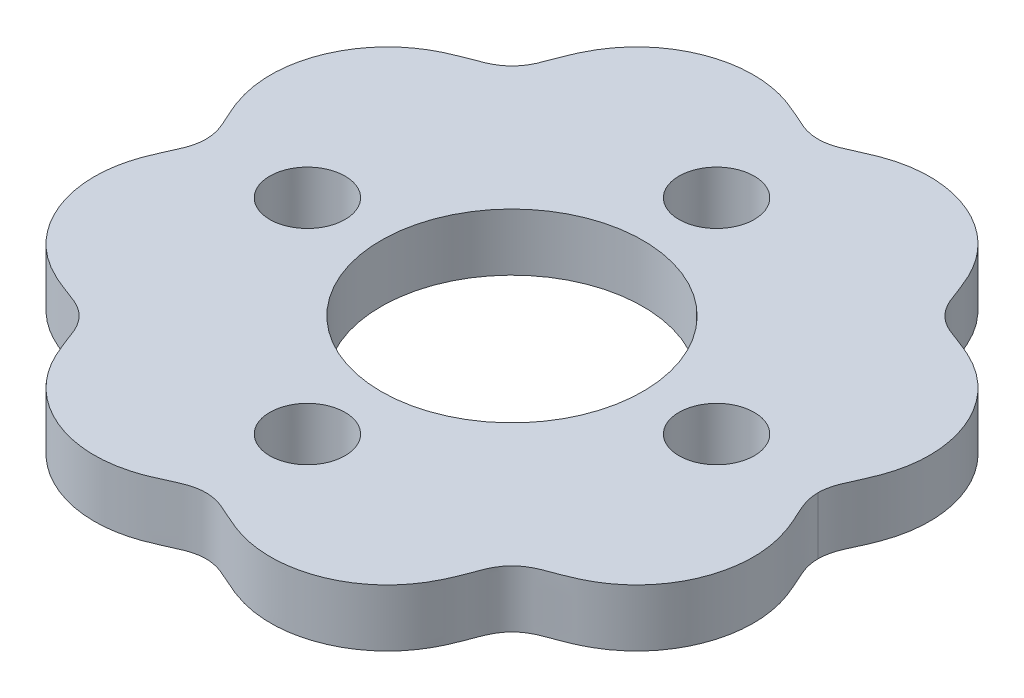
SolidWorks part; units mm, degrees
material "POM Acetal Copolymer"
ref_plane "Front Plane" through (0, 0, 0) normal (0, 0, 1) x (1, 0, 0)
ref_plane "Top Plane" through (0, 0, 0) normal (0, 1, 0) x (1, 0, 0)
ref_plane "Right Plane" through (0, 0, 0) normal (1, 0, 0) x (0, 0, -1)
sketch "Sketch2" plane through (0, 0, 0) normal (0, 1, 0) x (1, 0, 0)
  line L0 (-37.5, 0) -> (37.5, 0) construction
  spline S0 degree 4 number of poles 176 (36.9805, 20.0285) -> (-36.9805, 20.0285) construction
  spline S1 degree 4 number of poles 106 (37.5, 0) -> (-37.5, 0)
  spline S2 degree 4 number of poles 106 (37.5, 0) -> (-37.5, 0)
extrude "Boss-Extrude1" add sketch "Sketch2" along normal blind 7 contours S2 S1
sketch "Sketch3" plane through (0, 7, 0) normal (0, 1, 0) x (1, 0, 0)
  line L0 (0, 0) -> (37.5, 0) construction
  circle A0 centre (0, 0) radius 16
  circle A1 centre (25, 0) radius 4.5
  circle A3 centre (0, -25) radius 4.5
  circle A4 centre (-25, 0) radius 4.5
  circle A5 centre (0, 25) radius 4.5
  spline S0 degree 4 number of poles 106 (37.5, 0) -> (-37.5, 0) construction
  point P18 (0, 0)
  dimension "D1" = 32
  dimension "D2" = 9
  dimension "D4" = 25
  dimension "D5" = 4
extrude "Cut-Extrude1" cut sketch "Sketch3" against normal blind 7
sketch "Sketch4" plane through (0, 0, 0) normal (0, -1, 0) x (1, 0, 0)
  spline S2 degree 3 number of poles 181 (-37.4, 0) -> (37.4, 0)
  spline S3 degree 3 number of poles 181 (-37.4, 0) -> (37.4, 0)
  spline S4 degree 3 number of poles 174 (37.4, 0) -> (-37.4, 0)
  spline S5 degree 3 number of poles 174 (37.4, 0) -> (-37.4, 0)
  spline S9 degree 3 number of poles 172 (37.6, 0) -> (-37.6, 0)
  spline S10 degree 3 number of poles 172 (-37.6, 0) -> (37.6, 0)
  spline S11 degree 3 number of poles 172 (37.6, 0) -> (-37.6, 0)
  spline S12 degree 3 number of poles 172 (-37.6, 0) -> (37.6, 0)
  dimension "D1" = 0.1
  dimension "D2" = 0.1
sketch "Sketch5" plane through (0, 0, 0) normal (0, -1, 0) x (1, 0, 0)
  circle A1 centre (-25, 0) radius 4.6
  circle A2 centre (0, 25) radius 4.5
  circle A3 centre (0, 25) radius 4.5
  circle A4 centre (-25, 0) radius 4.5
  circle A5 centre (25, 0) radius 4.5
  circle A6 centre (25, 0) radius 4.5
  circle A7 centre (-25, 0) radius 4.5
  circle A11 centre (0, -25) radius 4.5
  circle A12 centre (0, -25) radius 4.5
  circle A13 centre (0, -25) radius 4.6
  circle A14 centre (25, 0) radius 4.6
  circle A15 centre (0, 25) radius 4.6
  dimension "D1" = 0
  dimension "D2" = 0
  dimension "D3" = 0
  dimension "D4" = 0
  dimension "D5" = 0.1
  dimension "D6" = 0.1
  dimension "D7" = 0.1
  dimension "D8" = 0.1
extrude "Cut-Extrude2" cut sketch "Sketch4" against normal up to surface (7 mm away) up to face at (25, 7, 4.5)
extrude "Cut-Extrude3" cut sketch "Sketch5" against normal up to surface (7 mm away) up to face at (0, 7, 16)
